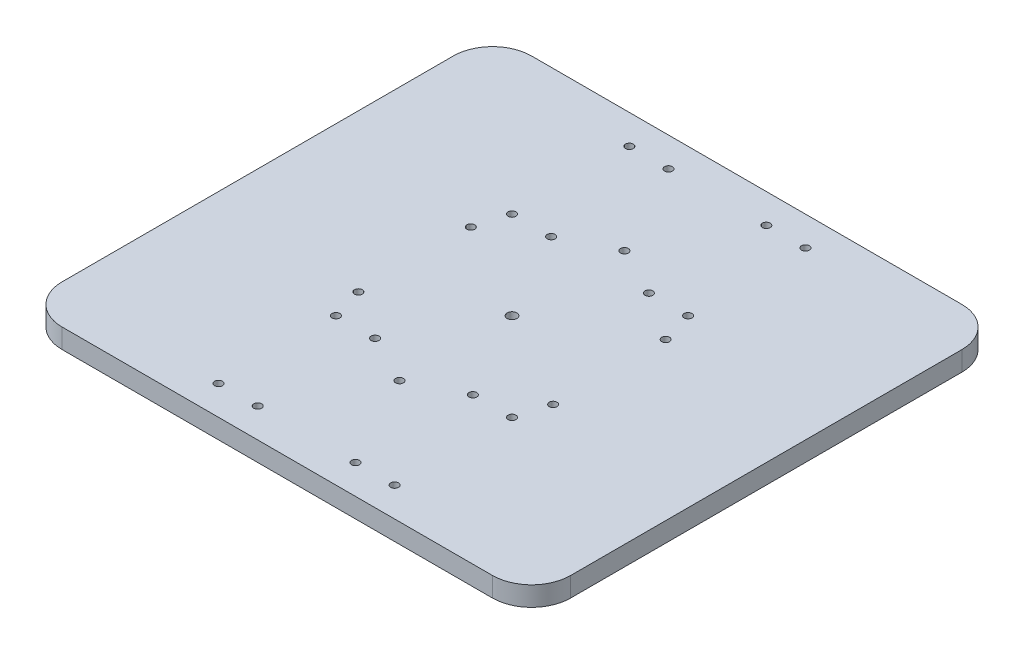
SolidWorks part; units mm, degrees
material "Acrylic (Medium-high impact)"
ref_plane "Front Plane" through (0, 0, 0) normal (0, 0, 1) x (1, 0, 0)
ref_plane "Top Plane" through (0, 0, 0) normal (0, 1, 0) x (1, 0, 0)
ref_plane "Right Plane" through (0, 0, 0) normal (1, 0, 0) x (0, 0, -1)
sketch "Sketch1" plane through (0, 0, 0) normal (0, 1, 0) x (1, 0, 0)
  line L1 (-130, -120) -> (130, -120)
  line L2 (-130, -120) -> (-130, 120)
  line L3 (-130, 120) -> (130, 120)
  line L4 (130, -120) -> (130, 120)
  line L5 (-130, -120) -> (130, 120) construction
  line L6 (-130, 120) -> (130, -120) construction
  point P0 (0, 0)
  dimension "D1" = 260
  dimension "D2" = 240
extrude "Boss-Extrude1" add sketch "Sketch1" along normal blind 10
fillet "Fillet3" radius 20 4 edges at (130, 5, -120) (130, 5, 120) (-130, 5, 120) (-130, 5, -120)
sketch "Sketch2" plane through (0, 10, 0) normal (0, 1, 0) x (1, 0, 0)
  line L0 (0, 0) -> (0, 99.0522) construction
  line L1 (0, 0) -> (95.8668, 0) construction
  line L2 (-71.4317, 105) -> (62.8964, 105) construction
  line L3 (-50, 70) -> (50, 70) construction
  line L4 (-50, 70) -> (-50, 80) construction
  line L5 (-50, 80) -> (50, 80) construction
  line L6 (50, 70) -> (50, 80) construction
  line L7 (-50, 70) -> (50, 80) construction
  line L8 (-50, 80) -> (50, 70) construction
  line L9 (-45, 113.4384) -> (-45, 38.3868) construction
  line L10 (45, 109.8532) -> (45, 34.8016) construction
  line L11 (-59.2418, 45) -> (87.7543, 45) construction
  line L12 (-25, 105.2559) -> (-25, 26.8047) construction
  line L13 (25, 103.2483) -> (25, 23.4072) construction
  circle A0 centre (-45, 105) radius 2
  circle A1 centre (45, 105) radius 2
  circle A2 centre (-45, 45) radius 2
  circle A3 centre (45, 45) radius 2
  circle A4 centre (0, 0) radius 57.5 construction
  circle A5 centre (0, 57.5) radius 2
  circle A6 centre (49.7965, 28.75) radius 2
  circle A7 centre (49.7965, -28.75) radius 2
  circle A8 centre (0, -57.5) radius 2
  circle A9 centre (-49.7965, -28.75) radius 2
  circle A10 centre (-49.7965, 28.75) radius 2
  circle A11 centre (-25, 105) radius 2
  circle A12 centre (25, 105) radius 2
  circle A13 centre (-25, 45) radius 2
  circle A14 centre (25, 45) radius 2
  circle A15 centre (-45, -45) radius 2
  circle A16 centre (-25, -45) radius 2
  circle A17 centre (25, -45) radius 2
  circle A18 centre (45, -45) radius 2
  circle A19 centre (45, -105) radius 2
  circle A20 centre (25, -105) radius 2
  circle A21 centre (-25, -105) radius 2
  circle A22 centre (-45, -105) radius 2
  circle A23 centre (0, 0) radius 2.5
  point P3 (0, 75)
  point P40 (0, 0)
  point P70 (0, 0)
  dimension "D8" = 4
  dimension "D9" = 4
  dimension "D10" = 4
  dimension "D11" = 4
  dimension "D12" = 115
  dimension "D13" = 4
  dimension "D17" = 4
  dimension "D18" = 4
  dimension "D19" = 4
  dimension "D20" = 4
  dimension "D21" = 5
  dimension "D1" = 10
  dimension "D2" = 100
  dimension "D3" = 70
  dimension "D4" = 25
  dimension "D5" = 5
  dimension "D6" = 5
  dimension "D7" = 25
  dimension "D15" = 20
  dimension "D16" = 20
  dimension "D14" = 6
sketch "Sketch3" plane through (0, 10, 0) normal (0, 1, 0) x (1, 0, 0)
  circle A1 centre (0, 0) radius 2.5
  circle A2 centre (0, 0) radius 2.5
  circle A3 centre (0, 57.5) radius 2
  circle A4 centre (0, 57.5) radius 2
  circle A5 centre (45, 45) radius 2
  circle A6 centre (45, 45) radius 2
  circle A7 centre (-45, 45) radius 2
  circle A8 centre (-45, 45) radius 2
  circle A9 centre (45, 105) radius 2
  circle A10 centre (45, 105) radius 2
  circle A11 centre (-45, 105) radius 2
  circle A12 centre (-45, 105) radius 2
  circle A13 centre (25, 105) radius 2
  circle A14 centre (25, 105) radius 2
  circle A15 centre (-25, 105) radius 2
  circle A16 centre (-25, 105) radius 2
  circle A17 centre (0, -57.5) radius 2
  circle A18 centre (0, -57.5) radius 2
  circle A19 centre (49.7965, -28.75) radius 2
  circle A20 centre (49.7965, -28.75) radius 2
  circle A21 centre (49.7965, 28.75) radius 2
  circle A22 centre (49.7965, 28.75) radius 2
  circle A23 centre (45, -105) radius 2
  circle A24 centre (45, -105) radius 2
  circle A25 centre (45, -45) radius 2
  circle A26 centre (45, -45) radius 2
  circle A27 centre (25, -45) radius 2
  circle A28 centre (25, -45) radius 2
  circle A29 centre (-25, -45) radius 2
  circle A30 centre (-25, -45) radius 2
  circle A31 centre (-45, -45) radius 2
  circle A32 centre (-45, -45) radius 2
  circle A33 centre (25, 45) radius 2
  circle A34 centre (25, 45) radius 2
  circle A35 centre (-25, 45) radius 2
  circle A36 centre (-25, 45) radius 2
  circle A37 centre (-49.7965, -28.75) radius 2
  circle A38 centre (-49.7965, -28.75) radius 2
  circle A39 centre (-45, -105) radius 2
  circle A40 centre (-45, -105) radius 2
  circle A41 centre (-25, -105) radius 2
  circle A42 centre (-25, -105) radius 2
  circle A43 centre (25, -105) radius 2
  circle A44 centre (25, -105) radius 2
  circle A45 centre (-49.7965, 28.75) radius 2
  circle A46 centre (-49.7965, 28.75) radius 2
  dimension "D1" = 0
  dimension "D2" = 0
  dimension "D3" = 0
  dimension "D4" = 0
  dimension "D5" = 0
  dimension "D6" = 0
  dimension "D7" = 0
  dimension "D8" = 0
  dimension "D9" = 0
  dimension "D10" = 0
  dimension "D11" = 0
  dimension "D12" = 0
  dimension "D13" = 0
  dimension "D14" = 0
  dimension "D15" = 0
  dimension "D16" = 0
  dimension "D17" = 0
  dimension "D18" = 0
  dimension "D19" = 0
  dimension "D20" = 0
  dimension "D21" = 0
  dimension "D22" = 0
  dimension "D23" = 0
extrude "Cut-Extrude2" cut sketch "Sketch3" against normal blind 10
